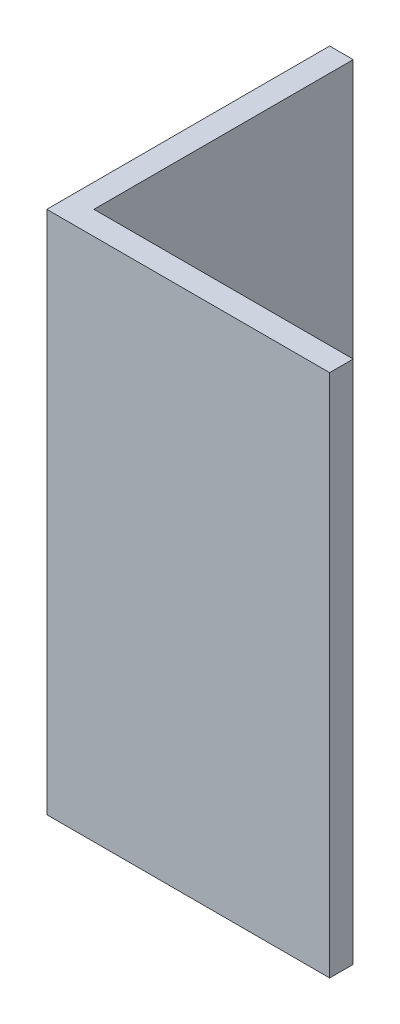
SolidWorks part; units mm, degrees
ref_plane "Front Plane" through (0, 0, 0) normal (0, 0, 1) x (1, 0, 0)
ref_plane "Top Plane" through (0, 0, 0) normal (0, 1, 0) x (1, 0, 0)
ref_plane "Right Plane" through (0, 0, 0) normal (1, 0, 0) x (0, 0, -1)
sketch "Sketch1" plane through (0, 0, 0) normal (0, 1, 0) x (1, 0, 0)
  line L0 (-30.994, 20.9399) -> (-30.994, -17.1601)
  line L1 (-30.994, -17.1601) -> (7.106, -17.1601)
  line L2 (7.106, -17.1601) -> (7.106, -13.9851)
  line L3 (7.106, -13.9851) -> (-27.819, -13.9851)
  line L4 (-27.819, -13.9851) -> (-27.819, 20.9399)
  line L5 (-30.994, 20.9399) -> (-27.819, 20.9399)
  dimension "D1" = 3.175
  dimension "D2" = 3.175
  dimension "D3" = 38.1
  dimension "D4" = 38.1
extrude "Boss-Extrude1" add sketch "Sketch1" along normal blind 70.612
